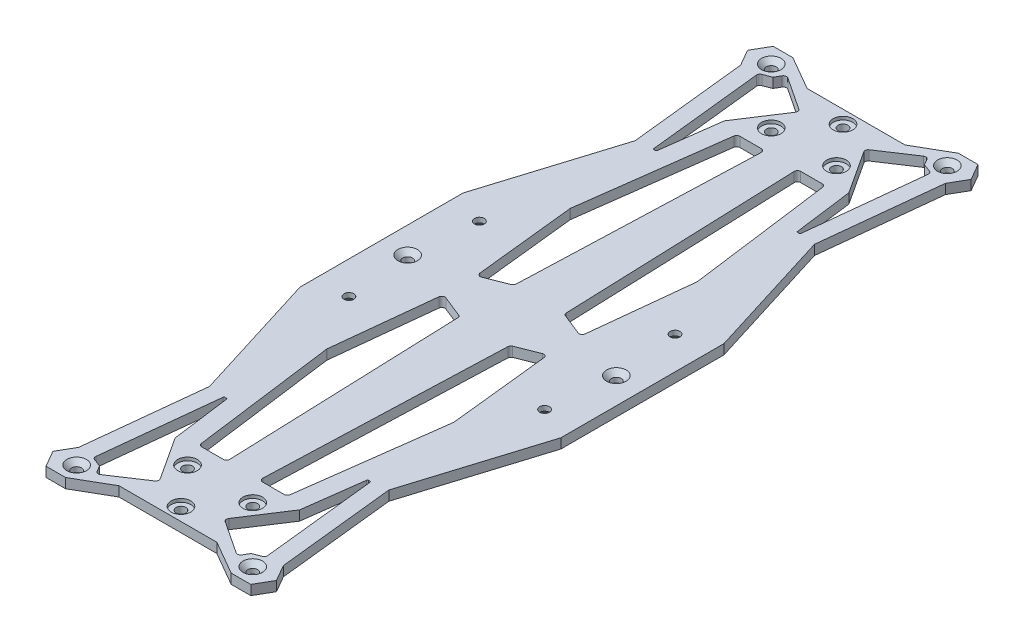
SolidWorks part; units mm, degrees
material "6061 合金"
ref_plane "前视基准面" through (0, 0, 0) normal (0, 0, 1) x (1, 0, 0)
ref_plane "上视基准面" through (0, 0, 0) normal (0, 1, 0) x (1, 0, 0)
ref_plane "右视基准面" through (0, 0, 0) normal (1, 0, 0) x (0, 0, -1)
sketch "草图1" plane through (0, 0, 0) normal (0, 1, 0) x (1, 0, 0)
  line L0 (0, 0) -> (0, 105.5) construction
  line L1 (-15, 105.5) -> (15, 105.5)
  line L2 (-40, 25) -> (40, 25)
  line L3 (15, 105.5) -> (40, 25)
  line L4 (40, 25) -> (40, -25)
  line L5 (-40, 25) -> (-40, -25)
  line L6 (-15, 105.5) -> (-40, 25)
  line L7 (-40, 0) -> (49960, 0) construction
  line L8 (-15, -105.5) -> (15, -105.5)
  line L9 (15, -105.5) -> (40, -25)
  line L10 (-40, -25) -> (40, -25)
  line L11 (-15, -105.5) -> (-40, -25)
  point P9 (0, 25)
  point P14 (40, 0)
  point P15 (-40, 0)
extrude "凸台-拉伸1" add sketch "草图1" along normal blind 3 contours L11 L8 L9 L10 | L5 L10 L4 L2 | L1 L6 L2 L3
sketch "草图2" plane through (0, 3, 0) normal (0, 1, 0) x (1, 0, 0)
  line L0 (0, 0) -> (0, 50000) construction
  line L1 (-15, 105.5) -> (15, 105.5) construction
  line L2 (-40, 0) -> (49960, 0) construction
  line L3 (-40, 25) -> (-40, -25) construction
  line L4 (40, 25) -> (40, -25) construction
  point P5 (0, 105.5)
  point P10 (-40, 0)
  point P13 (40, 0)
sketch "草图3" plane through (0, 3, 0) normal (0, 1, 0) x (1, 0, 0)
  line L0 (0, 0) -> (0, 107.9436) construction
  line L1 (0, -200000) -> (0, 250000) construction
  line L2 (0, 0) -> (78.3198, 0) construction
  line L3 (-200040, 0) -> (249960, 0) construction
  circle A1 centre (10, 89.5) radius 1.5
extrude "切除-拉伸1" cut sketch "草图3" against normal blind 3 contours A1
ref_plane "基准面1" through (0, 0, 0) normal (1, 0, 0) x (0, 0, -1)
ref_plane "基准面2" through (0, 0, 0) normal (0, 0, 1) x (1, 0, 0)
sketch "草图19" plane through (0, 3, 0) normal (0, 1, 0) x (1, 0, 0)
  line L0 (0, -200000) -> (0, 250000) construction
  circle A0 centre (0, 101.5) radius 1.5
extrude "切除-拉伸8" cut sketch "草图19" against normal blind 10
sketch "草图4" plane through (0, 3, 0) normal (0, 1, 0) x (1, 0, 0)
  circle A0 centre (0, 101.5) radius 3
  circle A1 centre (10, 89.5) radius 3
extrude "切除-拉伸2" cut sketch "草图4" against normal blind 1
sketch "草图6" plane through (0, 3, 0) normal (0, 1, 0) x (1, 0, 0)
  circle A0 centre (27, 106.5) radius 3
sketch "草图7" plane through (0, 3, 0) normal (0, 1, 0) x (1, 0, 0)
  line L0 (15, 105.5) -> (25.3923, 111.5)
  line L1 (25.3923, 111.5) -> (31.3923, 111.5)
  line L2 (31.3923, 111.5) -> (34.2791, 106.5)
  line L3 (27, 106.5) -> (34.2791, 106.5) construction
  line L4 (31.3923, 101.5) -> (34.2791, 106.5)
  line L5 (31.3923, 101.5) -> (27.5, 65.25)
  line L6 (15, 105.5) -> (40, 25) construction
  line L7 (15, 105.5) -> (27.5, 65.25)
extrude "凸台-拉伸2" add sketch "草图7" against normal blind 3 contours L5 L7 L0 L1 L2 L4
sketch "草图8" plane through (0, 3, 0) normal (0, 1, 0) x (1, 0, 0)
  circle A0 centre (27, 106.5) radius 1.5
extrude "切除-拉伸4" cut sketch "草图8" against normal blind 3 contours A0
sketch "草图9" plane through (0, 3, 0) normal (0, 1, 0) x (1, 0, 0)
  line L0 (31.3923, 101.5) -> (26.4209, 102.0338)
  line L1 (26.4209, 102.0338) -> (22.2287, 62.9914)
  line L2 (27.5, 65.25) -> (22.5286, 65.7838)
  line L3 (26.4209, 102.0338) -> (23.2433, 103.2222)
  line L4 (23.2433, 103.2222) -> (21.6692, 105.9485)
  line L5 (21.6692, 105.9485) -> (16.6582, 102.628)
  line L6 (22.5286, 65.7838) -> (21.5286, 65.7838)
  line L7 (21.5286, 65.7838) -> (16.6582, 102.628)
  line L8 (16.6582, 102.628) -> (9.9707, 98.1967)
  line L9 (10.3134, 97.6711) -> (9.9707, 98.1967)
  line L10 (10.3134, 97.6711) -> (19.0934, 84.2059)
extrude "切除-拉伸6" cut sketch "草图9" against normal through all and the other way through all
sketch "草图13" plane through (0, 3, 0) normal (0, 1, 0) x (1, 0, 0)
  line L0 (-200040, 0) -> (249960, 0) construction
  circle A0 centre (32, 0) radius 1.5
sketch "草图15" plane through (0, 0, 0) normal (0, -1, 0) x (1, 0, 0)
  circle A0 centre (-30, -20) radius 1.5
hole_wizard "M3 六角凹锥坑螺钉的锥形沉头孔2" positions "草图16" profile "草图17" countersink size "M3" standard "ISO" end condition through all
sketch "草图16" plane through (0, 0, 0) normal (0, -1, 0) x (-1, 0, 0)
  point P0 (30, 20)
sketch "草图17" plane through (-30, 0, -20) normal (1, 0, 0) x (0, 0, -1)
  line L0 (0, 0) -> (0, 3.0001)
  line L1 (0, 3.0001) -> (1.5, 3.0001)
  line L2 (1.5, 3.0001) -> (1.5, 1.5)
  line L3 (1.5, 1.5) -> (3, 0)
  line L5 (3, 0) -> (0, 0)
  line L6 (-1.5, 1.5) -> (-3, 0) construction
  line L11 (0, -6.35) -> (0, 107.95) construction
  dimension "通孔孔直径" = 3
  dimension "通孔孔深度" = 3.0001
  dimension "近端锥形沉头孔直径" = 6
  dimension "近端锥形沉头孔角度" = 90
hole_wizard "M3 六角凹锥坑螺钉的锥形沉头孔1" positions "草图11" profile "草图12" countersink size "M3" standard "ISO" end condition through all
sketch "草图11" plane through (0, 3, 0) normal (0, 1, 0) x (1, 0, 0)
  point P0 (27, 106.5)
  point P3 (32, 0)
sketch "草图12" plane through (27, 3, -106.5) normal (1, 0, 0) x (0, 0, 1)
  line L0 (0, 0) -> (0, 3)
  line L1 (0, 3) -> (1.5, 3)
  line L2 (1.5, 3) -> (1.5, 1.5)
  line L3 (1.5, 1.5) -> (3, 0)
  line L5 (3, 0) -> (0, 0)
  line L6 (-1.5, 1.5) -> (-3, 0) construction
  line L11 (0, -6.35) -> (0, 107.95) construction
  dimension "通孔孔直径" = 3
  dimension "通孔孔深度" = 3
  dimension "近端锥形沉头孔直径" = 6
  dimension "近端锥形沉头孔角度" = 90
mirror "镜向5" about plane through (0, 0, 0) normal (1, 0, 0) of "M3 六角凹锥坑螺钉的锥形沉头孔1"
sketch "草图18" plane through (0, 3, 0) normal (0, 1, 0) x (1, 0, 0)
  line L0 (22.5286, 65.7838) -> (15.4651, 0)
  line L1 (-200040, 0) -> (249960, 0) construction
  line L2 (27.5, 65.25) -> (20.4939, 0)
  line L3 (20.4939, 0) -> (15.4651, 0)
  line L5 (20.4939, 0) -> (24.4939, 0)
  line L6 (13.5, 82.5) -> (5, 82.5)
  line L7 (13.5, 82.5) -> (19.4723, 37.3201)
  line L10 (21.5286, 65.7838) -> (19.0934, 84.2059) construction
  line L11 (15.4651, 0) -> (8, 0)
  line L12 (8, 0) -> (5, 82.5)
  line L13 (7.6974, 8.3209) -> (16.002, 5)
  line L14 (7.8182, 5) -> (45.6767, 5) construction
  point P8 (16.002, 5)
extrude "切除-拉伸7" cut sketch "草图18" against normal through all and the other way through all
mirror "镜向6" about plane through (0, 0, 0) normal (1, 0, 0) of "切除-拉伸7", "M3 六角凹锥坑螺钉的锥形沉头孔1", "切除-拉伸6", "凸台-拉伸2", "切除-拉伸1", "切除-拉伸2", "M3 六角凹锥坑螺钉的锥形沉头孔2"
mirror "镜向7" about plane through (0, 0, 0) normal (0, 0, 1) of "切除-拉伸8", "镜向6", "切除-拉伸1", "切除-拉伸2", "凸台-拉伸2", "切除-拉伸6", "M3 六角凹锥坑螺钉的锥形沉头孔2", "M3 六角凹锥坑螺钉的锥形沉头孔1", "切除-拉伸7"
fillet "圆角1" radius 1 31 edges at (-26.4209, 1.5, -102.0338) (-21.6692, 1.5, -105.9485) (-9.9707, 1.5, -98.1967) (-13.5, 1.5, -82.5) (-5, 1.5, -82.5) (-19.4723, 1.5, -37.3201) (-7.6974, 1.5, -8.3209) (-16.002, 1.5, -5) (13.5, 1.5, -82.5) (5, 1.5, -82.5) (7.6974, 1.5, -8.3209) (16.002, 1.5, -5) (26.4209, 1.5, -102.0338) (21.6692, 1.5, -105.9485) (9.9707, 1.5, -98.1967) (7.6974, 1.5, 8.3209) (16.002, 1.5, 5) (19.4723, 1.5, 37.3201) (13.5, 1.5, 82.5) (5, 1.5, 82.5) (9.9707, 1.5, 98.1967) (21.6692, 1.5, 105.9485) (26.4209, 1.5, 102.0338) (-9.9707, 1.5, 98.1967) (-21.6692, 1.5, 105.9485) (-26.4209, 1.5, 102.0338) (-13.5, 1.5, 82.5) (-5, 1.5, 82.5) (-19.4723, 1.5, 37.3201) (-16.002, 1.5, 5) (-7.6974, 1.5, 8.3209)
fillet "圆角2" radius 0.3 8 edges at (-22.5286, 1.5, -65.7838) (-21.5286, 1.5, -65.7838) (22.5286, 1.5, -65.7838) (21.5286, 1.5, -65.7838) (21.5286, 1.5, 65.7838) (22.5286, 1.5, 65.7838) (-21.5286, 1.5, 65.7838) (-22.5286, 1.5, 65.7838)
